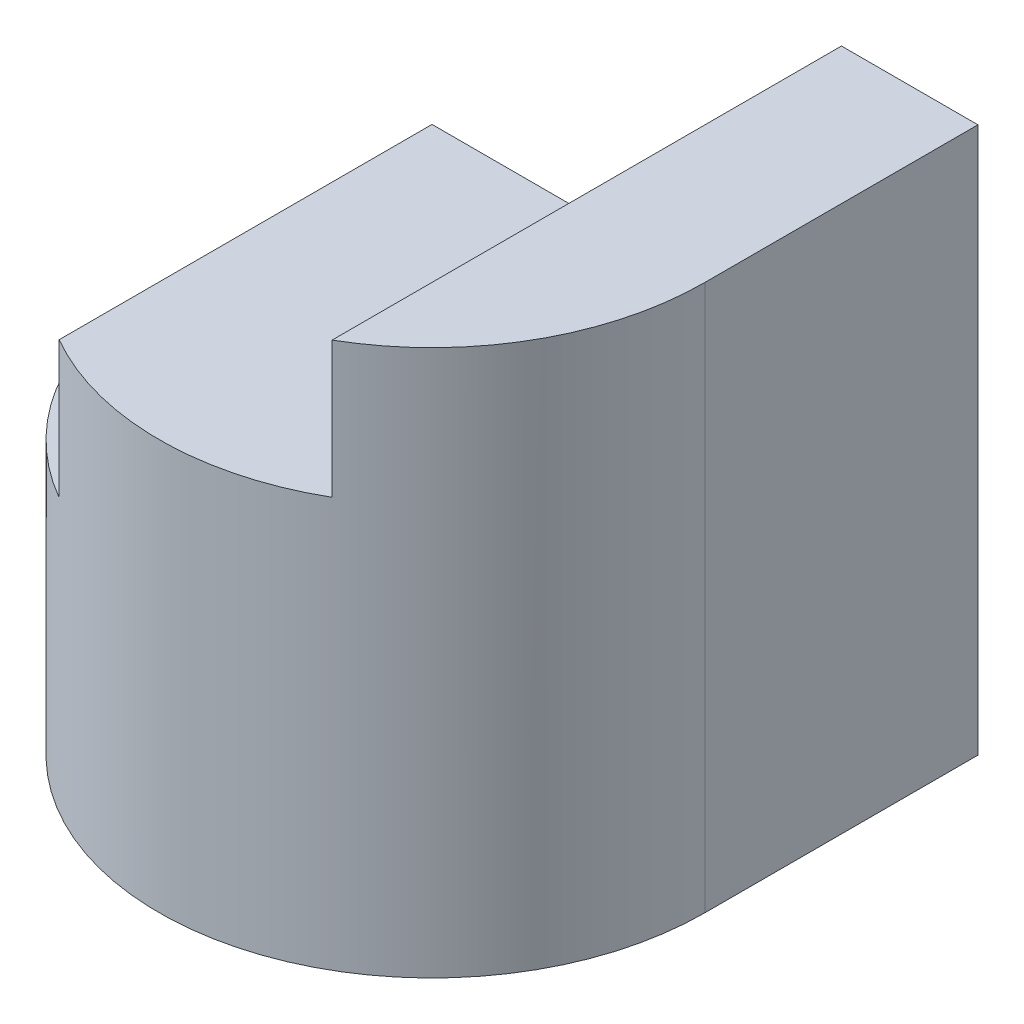
SolidWorks part; units mm, degrees
ref_plane "Front" through (0, 0, 0) normal (0, 0, 1) x (1, 0, 0)
ref_plane "Top" through (0, 0, 0) normal (0, 1, 0) x (1, 0, 0)
ref_plane "Right" through (0, 0, 0) normal (1, 0, 0) x (0, 0, -1)
sketch "Sketch1" plane through (0, 0, 0) normal (0, 1, 0) x (1, 0, 0)
  line L0 (-2, 2) -> (-2, 0)
  line L1 (2, 0) -> (2, 2)
  line L2 (2, 2) -> (1, 2)
  line L3 (1, 2) -> (1, 1)
  line L4 (1, 1) -> (-1, 1)
  line L5 (-1, 1) -> (-1, 2)
  line L6 (-1, 2) -> (-2, 2)
  arc A0 (-2, 0) -> (2, 0) centre (0, 0) ccw
  dimension "D7" = 0
  dimension "D1" = 2
  dimension "D2" = 1
  dimension "D3" = 2
  dimension "D4" = 1
  dimension "D5" = 1
  dimension "D6" = 1
extrude "Boss-Extrude1" add sketch "Sketch1" along normal blind 4
sketch "Sketch2" plane through (0, 0, -2) normal (0, 0, -1) x (-1, 0, 0)
  line L0 (-1, 4) -> (-1, 3.0025)
  line L1 (-1, 3.0025) -> (1, 3.0025)
  line L2 (1, 3.0025) -> (1, 2)
  line L3 (1, 2) -> (2, 2)
  line L4 (2, 4) -> (2, 0) construction
  line L5 (2, 2) -> (2, 4)
  line L6 (2, 4) -> (-1, 4)
  dimension "D1" = 2
  dimension "D2" = 2
extrude "Cut-Extrude1" cut sketch "Sketch2" against normal blind 4
